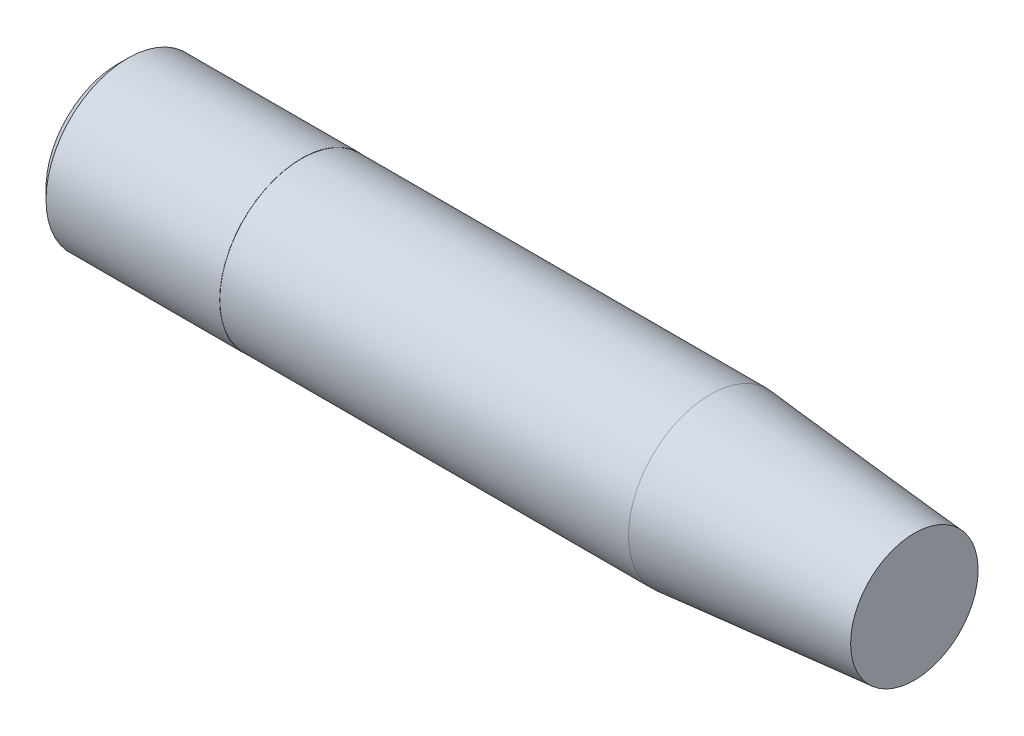
SolidWorks part; units mm, degrees
material "Brass"
ref_plane "Front Plane" through (0, 0, 0) normal (0, 0, 1) x (1, 0, 0)
ref_plane "Top Plane" through (0, 0, 0) normal (0, 1, 0) x (1, 0, 0)
ref_plane "Right Plane" through (0, 0, 0) normal (1, 0, 0) x (0, 0, -1)
sketch "Sketch1" plane through (0, 0, 0) normal (0, 0, 1) x (1, 0, 0)
  line L0 (0, 2.0025) -> (0, 3.5)
  line L1 (0, 3.5) -> (-1, 3.5)
  line L2 (-1, 3.5) -> (-1, 0)
  line L3 (-1, 0) -> (19.5, 0)
  line L4 (19.5, 0) -> (19.5, 1.5601)
  line L5 (19.5, 1.5601) -> (14.5, 1.9975)
  line L6 (14.5, 1.9975) -> (4.5, 1.9975)
  line L7 (4.5, 1.9975) -> (4.5, 2.0025)
  line L8 (4.5, 2.0025) -> (0, 2.0025)
  line L9 (-30.1671, 0) -> (-9.6388, 0) construction
  dimension "D1" = 4.5
  dimension "D2" = 10
  dimension "D3" = 5
  dimension "D4" = 5
  dimension "D5" = 3.995
  dimension "D6" = 4.005
  dimension "D7" = 1
  dimension "D8" = 7
revolve "Revolve1" add sketch "Sketch1" angle 360 about L9
fillet "Fillet1" radius 0.25 1 edges at (0, 0, 2.0025)
sketch "Sketch2" plane through (0, 0, 0) normal (0, 0, 1) x (1, 0, 0)
  line L0 (0.25, 2.0025) -> (0, 1.7525)
  line L1 (0, -2.2525) -> (0, 2.2525) construction
  line L2 (0, 1.7525) -> (0, 0)
  line L3 (0, 0) -> (-1, 0)
  line L4 (-1, 3.5) -> (-1, -3.5) construction
  line L5 (-1, 0) -> (-1, 3.5)
  line L6 (-1, 3.5) -> (0, 3.5)
  line L7 (0, 3.5) -> (0.25, 2.0025)
  dimension "D1" = 45
revolve "Cut-Revolve1" cut sketch "Sketch2" angle 360 about L3
